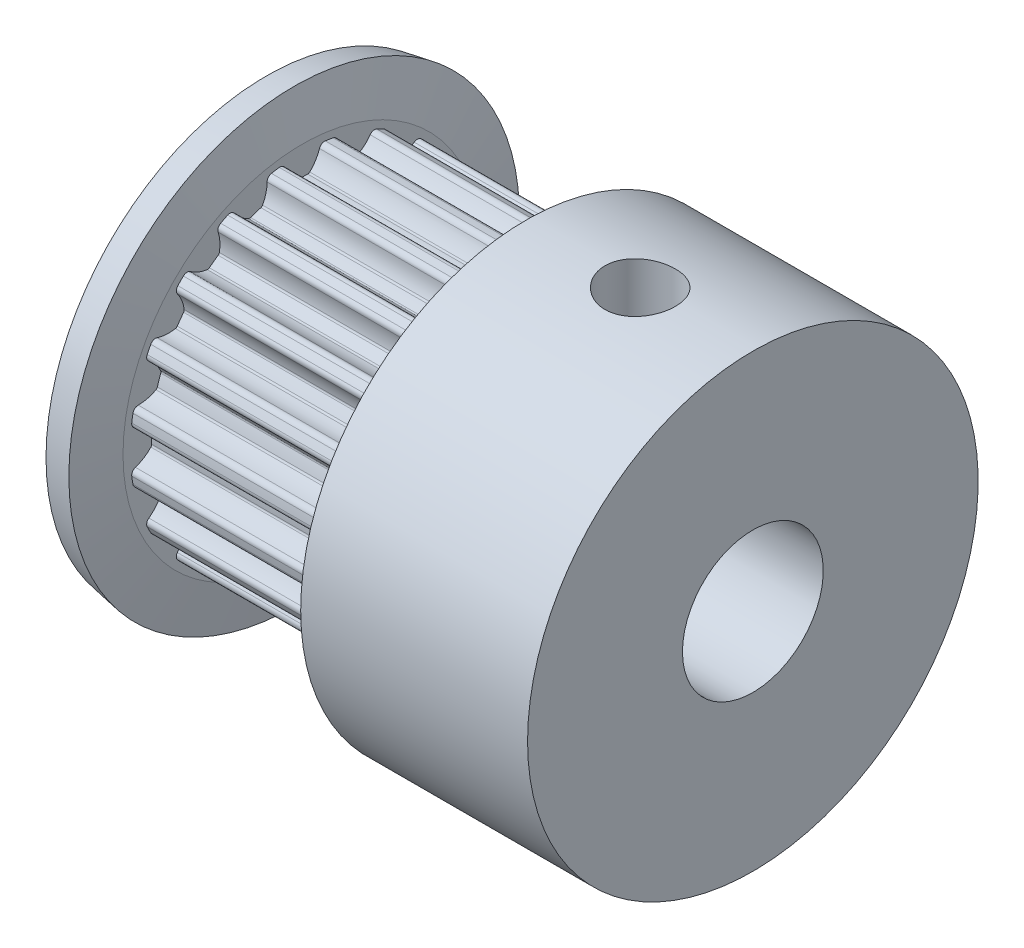
SolidWorks part; units mm, degrees
material "6061 Alloy"
ref_plane "Front Plane" through (0, 0, 0) normal (0, 0, 1) x (1, 0, 0)
ref_plane "Top Plane" through (0, 0, 0) normal (0, 1, 0) x (1, 0, 0)
ref_plane "Right Plane" through (0, 0, 0) normal (1, 0, 0) x (0, 0, -1)
ref_plane "Plane1" through (0, 0, 0) normal (0, 0, 1) x (1, 0, 0)
sketch "Sketch1" plane through (0, 0, 0) normal (0, 0, 1) x (1, 0, 0)
  line L0 (0, 5) -> (0, 2.5)
  line L1 (0, 2.5) -> (18, 2.5)
  line L2 (18, 2.5) -> (18, 8)
  line L3 (18, 8) -> (9.944, 8)
  line L4 (9.944, 8) -> (9, 6.365)
  line L5 (9, 6.365) -> (9, 6.11)
  line L6 (9, 6.11) -> (2, 6.11)
  line L7 (2, 6.11) -> (2, 6.365)
  line L8 (2, 6.365) -> (1.7117, 8)
  line L9 (1.7117, 8) -> (0.7269, 7.8264)
  line L10 (0.7269, 7.8264) -> (1, 6.2775)
  line L11 (1, 6.2775) -> (1, 5)
  line L12 (1, 5) -> (0, 5)
  line L13 (19, 0) -> (0, 0) construction
  dimension "D1" = 10
  dimension "D2" = 1
  dimension "D3" = 8
  dimension "D4" = 6.365
  dimension "D5" = 18
  dimension "D6" = 7
  dimension "D7" = 9
  dimension "D8" = 30
revolve "Revolve1" add sketch "Sketch1" angle 360 about L13
ref_plane "Plane2" through (2, 0, 0) normal (1, 0, 0) x (0, 0, -1)
sketch "Sketch2" plane through (2, 0, 0) normal (1, 0, 0) x (0, 0, -1)
  line L0 (0.8173, 6.0551) -> (0.8173, 8.1467)
  line L1 (0.8173, 8.1467) -> (-0.8173, 8.1467)
  line L2 (-0.8173, 8.1467) -> (-0.8173, 6.0551)
  arc A0 (-0.8173, 6.0551) -> (-0.6111, 5.9251) centre (-0.7919, 5.8668) cw
  arc A1 (-0.6111, 5.9251) -> (-0.2658, 5.3742) centre (0.65, 6.3317) ccw
  arc A2 (-0.2658, 5.3742) -> (-0.1931, 5.3465) centre (-0.1967, 5.4464) ccw
  arc A3 (-0.1931, 5.3465) -> (0.1931, 5.3465) centre (0, 0) cw
  arc A4 (0.1931, 5.3465) -> (0.2658, 5.3742) centre (0.1967, 5.4464) ccw
  arc A5 (0.2658, 5.3742) -> (0.6111, 5.9251) centre (-0.65, 6.3317) ccw
  arc A6 (0.6111, 5.9251) -> (0.8173, 6.0551) centre (0.7919, 5.8668) cw
extrude "Cut-Extrude1" cut sketch "Sketch2" along normal blind 7
ref_plane "Plane3" through (2, 0, 0) normal (1, 0, 0) x (0, 0, -1)
sketch "Sketch3" plane through (2, 0, 0) normal (1, 0, 0) x (0, 0, -1)
  line L0 (-1.0938, 6.0113) -> (-1.7401, 8.0005)
  line L1 (-1.7401, 8.0005) -> (-3.2948, 7.4954)
  line L2 (-3.2948, 7.4954) -> (-2.6484, 5.5062)
  arc A0 (-2.6484, 5.5062) -> (-2.4121, 5.4463) centre (-2.5661, 5.3349) cw
  arc A1 (-2.4121, 5.4463) -> (-1.9135, 5.029) centre (-1.3384, 6.2227) ccw
  arc A2 (-1.9135, 5.029) -> (-1.8358, 5.0252) centre (-1.8701, 5.1191) ccw
  arc A3 (-1.8358, 5.0252) -> (-1.4685, 5.1445) centre (0, 0) cw
  arc A4 (-1.4685, 5.1445) -> (-1.4079, 5.1933) centre (-1.496, 5.2407) ccw
  arc A5 (-1.4079, 5.1933) -> (-1.2498, 5.8239) centre (-2.5748, 5.821) ccw
  arc A6 (-1.2498, 5.8239) -> (-1.0938, 6.0113) centre (-1.0598, 5.8244) cw
extrude "Cut-Extrude2" cut sketch "Sketch3" along normal blind 7
ref_plane "Plane4" through (2, 0, 0) normal (1, 0, 0) x (0, 0, -1)
sketch "Sketch4" plane through (2, 0, 0) normal (1, 0, 0) x (0, 0, -1)
  line L0 (-2.8979, 5.3791) -> (-4.1273, 7.0712)
  line L1 (-4.1273, 7.0712) -> (-5.4497, 6.1104)
  line L2 (-5.4497, 6.1104) -> (-4.2203, 4.4183)
  arc A0 (-4.2203, 4.4183) -> (-3.9771, 4.4343) centre (-4.0891, 4.2809) cw
  arc A1 (-3.9771, 4.4343) -> (-3.3739, 4.1916) centre (-3.1958, 5.5045) ccw
  arc A2 (-3.3739, 4.1916) -> (-3.2988, 4.2119) centre (-3.3605, 4.2906) ccw
  arc A3 (-3.2988, 4.2119) -> (-2.9864, 4.4389) centre (0, 0) cw
  arc A4 (-2.9864, 4.4389) -> (-2.9438, 4.5041) centre (-3.0422, 4.5219) ccw
  arc A5 (-2.9438, 4.5041) -> (-2.9883, 5.1527) centre (-4.2476, 4.7404) ccw
  arc A6 (-2.9883, 5.1527) -> (-2.8979, 5.3791) centre (-2.8078, 5.2118) cw
extrude "Cut-Extrude3" cut sketch "Sketch4" along normal blind 7
ref_plane "Plane5" through (2, 0, 0) normal (1, 0, 0) x (0, 0, -1)
sketch "Sketch5" plane through (2, 0, 0) normal (1, 0, 0) x (0, 0, -1)
  line L0 (-4.4183, 4.2203) -> (-6.1104, 5.4497)
  line L1 (-6.1104, 5.4497) -> (-7.0712, 4.1273)
  line L2 (-7.0712, 4.1273) -> (-5.3791, 2.8979)
  arc A0 (-5.3791, 2.8979) -> (-5.1527, 2.9883) centre (-5.2118, 2.8078) cw
  arc A1 (-5.1527, 2.9883) -> (-4.5041, 2.9438) centre (-4.7404, 4.2476) ccw
  arc A2 (-4.5041, 2.9438) -> (-4.4389, 2.9864) centre (-4.5219, 3.0422) ccw
  arc A3 (-4.4389, 2.9864) -> (-4.2119, 3.2988) centre (0, 0) cw
  arc A4 (-4.2119, 3.2988) -> (-4.1916, 3.3739) centre (-4.2906, 3.3605) ccw
  arc A5 (-4.1916, 3.3739) -> (-4.4343, 3.9771) centre (-5.5045, 3.1958) ccw
  arc A6 (-4.4343, 3.9771) -> (-4.4183, 4.2203) centre (-4.2809, 4.0891) cw
extrude "Cut-Extrude4" cut sketch "Sketch5" along normal blind 7
ref_plane "Plane6" through (2, 0, 0) normal (1, 0, 0) x (0, 0, -1)
sketch "Sketch6" plane through (2, 0, 0) normal (1, 0, 0) x (0, 0, -1)
  line L0 (-5.5062, 2.6484) -> (-7.4954, 3.2948)
  line L1 (-7.4954, 3.2948) -> (-8.0005, 1.7401)
  line L2 (-8.0005, 1.7401) -> (-6.0113, 1.0938)
  arc A0 (-6.0113, 1.0938) -> (-5.8239, 1.2498) centre (-5.8244, 1.0598) cw
  arc A1 (-5.8239, 1.2498) -> (-5.1933, 1.4079) centre (-5.821, 2.5748) ccw
  arc A2 (-5.1933, 1.4079) -> (-5.1445, 1.4685) centre (-5.2407, 1.496) ccw
  arc A3 (-5.1445, 1.4685) -> (-5.0252, 1.8358) centre (0, 0) cw
  arc A4 (-5.0252, 1.8358) -> (-5.029, 1.9135) centre (-5.1191, 1.8701) ccw
  arc A5 (-5.029, 1.9135) -> (-5.4463, 2.4121) centre (-6.2227, 1.3384) ccw
  arc A6 (-5.4463, 2.4121) -> (-5.5062, 2.6484) centre (-5.3349, 2.5661) cw
extrude "Cut-Extrude5" cut sketch "Sketch6" along normal blind 7
ref_plane "Plane7" through (2, 0, 0) normal (1, 0, 0) x (0, 0, -1)
sketch "Sketch7" plane through (2, 0, 0) normal (1, 0, 0) x (0, 0, -1)
  line L0 (-6.0551, 0.8173) -> (-8.1467, 0.8173)
  line L1 (-8.1467, 0.8173) -> (-8.1467, -0.8173)
  line L2 (-8.1467, -0.8173) -> (-6.0551, -0.8173)
  arc A0 (-6.0551, -0.8173) -> (-5.9251, -0.6111) centre (-5.8668, -0.7919) cw
  arc A1 (-5.9251, -0.6111) -> (-5.3742, -0.2658) centre (-6.3317, 0.65) ccw
  arc A2 (-5.3742, -0.2658) -> (-5.3465, -0.1931) centre (-5.4464, -0.1967) ccw
  arc A3 (-5.3465, -0.1931) -> (-5.3465, 0.1931) centre (0, 0) cw
  arc A4 (-5.3465, 0.1931) -> (-5.3742, 0.2658) centre (-5.4464, 0.1967) ccw
  arc A5 (-5.3742, 0.2658) -> (-5.9251, 0.6111) centre (-6.3317, -0.65) ccw
  arc A6 (-5.9251, 0.6111) -> (-6.0551, 0.8173) centre (-5.8668, 0.7919) cw
extrude "Cut-Extrude6" cut sketch "Sketch7" along normal blind 7
ref_plane "Plane8" through (2, 0, 0) normal (1, 0, 0) x (0, 0, -1)
sketch "Sketch8" plane through (2, 0, 0) normal (1, 0, 0) x (0, 0, -1)
  line L0 (-6.0113, -1.0938) -> (-8.0005, -1.7401)
  line L1 (-8.0005, -1.7401) -> (-7.4954, -3.2948)
  line L2 (-7.4954, -3.2948) -> (-5.5062, -2.6484)
  arc A0 (-5.5062, -2.6484) -> (-5.4463, -2.4121) centre (-5.3349, -2.5661) cw
  arc A1 (-5.4463, -2.4121) -> (-5.029, -1.9135) centre (-6.2227, -1.3384) ccw
  arc A2 (-5.029, -1.9135) -> (-5.0252, -1.8358) centre (-5.1191, -1.8701) ccw
  arc A3 (-5.0252, -1.8358) -> (-5.1445, -1.4685) centre (0, 0) cw
  arc A4 (-5.1445, -1.4685) -> (-5.1933, -1.4079) centre (-5.2407, -1.496) ccw
  arc A5 (-5.1933, -1.4079) -> (-5.8239, -1.2498) centre (-5.821, -2.5748) ccw
  arc A6 (-5.8239, -1.2498) -> (-6.0113, -1.0938) centre (-5.8244, -1.0598) cw
extrude "Cut-Extrude7" cut sketch "Sketch8" along normal blind 7
ref_plane "Plane9" through (2, 0, 0) normal (1, 0, 0) x (0, 0, -1)
sketch "Sketch9" plane through (2, 0, 0) normal (1, 0, 0) x (0, 0, -1)
  line L0 (-5.3791, -2.8979) -> (-7.0712, -4.1273)
  line L1 (-7.0712, -4.1273) -> (-6.1104, -5.4497)
  line L2 (-6.1104, -5.4497) -> (-4.4183, -4.2203)
  arc A0 (-4.4183, -4.2203) -> (-4.4343, -3.9771) centre (-4.2809, -4.0891) cw
  arc A1 (-4.4343, -3.9771) -> (-4.1916, -3.3739) centre (-5.5045, -3.1958) ccw
  arc A2 (-4.1916, -3.3739) -> (-4.2119, -3.2988) centre (-4.2906, -3.3605) ccw
  arc A3 (-4.2119, -3.2988) -> (-4.4389, -2.9864) centre (0, 0) cw
  arc A4 (-4.4389, -2.9864) -> (-4.5041, -2.9438) centre (-4.5219, -3.0422) ccw
  arc A5 (-4.5041, -2.9438) -> (-5.1527, -2.9883) centre (-4.7404, -4.2476) ccw
  arc A6 (-5.1527, -2.9883) -> (-5.3791, -2.8979) centre (-5.2118, -2.8078) cw
extrude "Cut-Extrude8" cut sketch "Sketch9" along normal blind 7
ref_plane "Plane10" through (2, 0, 0) normal (1, 0, 0) x (0, 0, -1)
sketch "Sketch10" plane through (2, 0, 0) normal (1, 0, 0) x (0, 0, -1)
  line L0 (-4.2203, -4.4183) -> (-5.4497, -6.1104)
  line L1 (-5.4497, -6.1104) -> (-4.1273, -7.0712)
  line L2 (-4.1273, -7.0712) -> (-2.8979, -5.3791)
  arc A0 (-2.8979, -5.3791) -> (-2.9883, -5.1527) centre (-2.8078, -5.2118) cw
  arc A1 (-2.9883, -5.1527) -> (-2.9438, -4.5041) centre (-4.2476, -4.7404) ccw
  arc A2 (-2.9438, -4.5041) -> (-2.9864, -4.4389) centre (-3.0422, -4.5219) ccw
  arc A3 (-2.9864, -4.4389) -> (-3.2988, -4.2119) centre (0, 0) cw
  arc A4 (-3.2988, -4.2119) -> (-3.3739, -4.1916) centre (-3.3605, -4.2906) ccw
  arc A5 (-3.3739, -4.1916) -> (-3.9771, -4.4343) centre (-3.1958, -5.5045) ccw
  arc A6 (-3.9771, -4.4343) -> (-4.2203, -4.4183) centre (-4.0891, -4.2809) cw
extrude "Cut-Extrude9" cut sketch "Sketch10" along normal blind 7
ref_plane "Plane11" through (2, 0, 0) normal (1, 0, 0) x (0, 0, -1)
sketch "Sketch11" plane through (2, 0, 0) normal (1, 0, 0) x (0, 0, -1)
  line L0 (-2.6484, -5.5062) -> (-3.2948, -7.4954)
  line L1 (-3.2948, -7.4954) -> (-1.7401, -8.0005)
  line L2 (-1.7401, -8.0005) -> (-1.0938, -6.0113)
  arc A0 (-1.0938, -6.0113) -> (-1.2498, -5.8239) centre (-1.0598, -5.8244) cw
  arc A1 (-1.2498, -5.8239) -> (-1.4079, -5.1933) centre (-2.5748, -5.821) ccw
  arc A2 (-1.4079, -5.1933) -> (-1.4685, -5.1445) centre (-1.496, -5.2407) ccw
  arc A3 (-1.4685, -5.1445) -> (-1.8358, -5.0252) centre (0, 0) cw
  arc A4 (-1.8358, -5.0252) -> (-1.9135, -5.029) centre (-1.8701, -5.1191) ccw
  arc A5 (-1.9135, -5.029) -> (-2.4121, -5.4463) centre (-1.3384, -6.2227) ccw
  arc A6 (-2.4121, -5.4463) -> (-2.6484, -5.5062) centre (-2.5661, -5.3349) cw
extrude "Cut-Extrude10" cut sketch "Sketch11" along normal blind 7
ref_plane "Plane12" through (2, 0, 0) normal (1, 0, 0) x (0, 0, -1)
sketch "Sketch12" plane through (2, 0, 0) normal (1, 0, 0) x (0, 0, -1)
  line L0 (-0.8173, -6.0551) -> (-0.8173, -8.1467)
  line L1 (-0.8173, -8.1467) -> (0.8173, -8.1467)
  line L2 (0.8173, -8.1467) -> (0.8173, -6.0551)
  arc A0 (0.8173, -6.0551) -> (0.6111, -5.9251) centre (0.7919, -5.8668) cw
  arc A1 (0.6111, -5.9251) -> (0.2658, -5.3742) centre (-0.65, -6.3317) ccw
  arc A2 (0.2658, -5.3742) -> (0.1931, -5.3465) centre (0.1967, -5.4464) ccw
  arc A3 (0.1931, -5.3465) -> (-0.1931, -5.3465) centre (0, 0) cw
  arc A4 (-0.1931, -5.3465) -> (-0.2658, -5.3742) centre (-0.1967, -5.4464) ccw
  arc A5 (-0.2658, -5.3742) -> (-0.6111, -5.9251) centre (0.65, -6.3317) ccw
  arc A6 (-0.6111, -5.9251) -> (-0.8173, -6.0551) centre (-0.7919, -5.8668) cw
extrude "Cut-Extrude11" cut sketch "Sketch12" along normal blind 7
ref_plane "Plane13" through (2, 0, 0) normal (1, 0, 0) x (0, 0, -1)
sketch "Sketch13" plane through (2, 0, 0) normal (1, 0, 0) x (0, 0, -1)
  line L0 (1.0938, -6.0113) -> (1.7401, -8.0005)
  line L1 (1.7401, -8.0005) -> (3.2948, -7.4954)
  line L2 (3.2948, -7.4954) -> (2.6484, -5.5062)
  arc A0 (2.6484, -5.5062) -> (2.4121, -5.4463) centre (2.5661, -5.3349) cw
  arc A1 (2.4121, -5.4463) -> (1.9135, -5.029) centre (1.3384, -6.2227) ccw
  arc A2 (1.9135, -5.029) -> (1.8358, -5.0252) centre (1.8701, -5.1191) ccw
  arc A3 (1.8358, -5.0252) -> (1.4685, -5.1445) centre (0, 0) cw
  arc A4 (1.4685, -5.1445) -> (1.4079, -5.1933) centre (1.496, -5.2407) ccw
  arc A5 (1.4079, -5.1933) -> (1.2498, -5.8239) centre (2.5748, -5.821) ccw
  arc A6 (1.2498, -5.8239) -> (1.0938, -6.0113) centre (1.0598, -5.8244) cw
extrude "Cut-Extrude12" cut sketch "Sketch13" along normal blind 7
ref_plane "Plane14" through (2, 0, 0) normal (1, 0, 0) x (0, 0, -1)
sketch "Sketch14" plane through (2, 0, 0) normal (1, 0, 0) x (0, 0, -1)
  line L0 (2.8979, -5.3791) -> (4.1273, -7.0712)
  line L1 (4.1273, -7.0712) -> (5.4497, -6.1104)
  line L2 (5.4497, -6.1104) -> (4.2203, -4.4183)
  arc A0 (4.2203, -4.4183) -> (3.9771, -4.4343) centre (4.0891, -4.2809) cw
  arc A1 (3.9771, -4.4343) -> (3.3739, -4.1916) centre (3.1958, -5.5045) ccw
  arc A2 (3.3739, -4.1916) -> (3.2988, -4.2119) centre (3.3605, -4.2906) ccw
  arc A3 (3.2988, -4.2119) -> (2.9864, -4.4389) centre (0, 0) cw
  arc A4 (2.9864, -4.4389) -> (2.9438, -4.5041) centre (3.0422, -4.5219) ccw
  arc A5 (2.9438, -4.5041) -> (2.9883, -5.1527) centre (4.2476, -4.7404) ccw
  arc A6 (2.9883, -5.1527) -> (2.8979, -5.3791) centre (2.8078, -5.2118) cw
extrude "Cut-Extrude13" cut sketch "Sketch14" along normal blind 7
ref_plane "Plane15" through (2, 0, 0) normal (1, 0, 0) x (0, 0, -1)
sketch "Sketch15" plane through (2, 0, 0) normal (1, 0, 0) x (0, 0, -1)
  line L0 (4.4183, -4.2203) -> (6.1104, -5.4497)
  line L1 (6.1104, -5.4497) -> (7.0712, -4.1273)
  line L2 (7.0712, -4.1273) -> (5.3791, -2.8979)
  arc A0 (5.3791, -2.8979) -> (5.1527, -2.9883) centre (5.2118, -2.8078) cw
  arc A1 (5.1527, -2.9883) -> (4.5041, -2.9438) centre (4.7404, -4.2476) ccw
  arc A2 (4.5041, -2.9438) -> (4.4389, -2.9864) centre (4.5219, -3.0422) ccw
  arc A3 (4.4389, -2.9864) -> (4.2119, -3.2988) centre (0, 0) cw
  arc A4 (4.2119, -3.2988) -> (4.1916, -3.3739) centre (4.2906, -3.3605) ccw
  arc A5 (4.1916, -3.3739) -> (4.4343, -3.9771) centre (5.5045, -3.1958) ccw
  arc A6 (4.4343, -3.9771) -> (4.4183, -4.2203) centre (4.2809, -4.0891) cw
extrude "Cut-Extrude14" cut sketch "Sketch15" along normal blind 7
ref_plane "Plane16" through (2, 0, 0) normal (1, 0, 0) x (0, 0, -1)
sketch "Sketch16" plane through (2, 0, 0) normal (1, 0, 0) x (0, 0, -1)
  line L0 (5.5062, -2.6484) -> (7.4954, -3.2948)
  line L1 (7.4954, -3.2948) -> (8.0005, -1.7401)
  line L2 (8.0005, -1.7401) -> (6.0113, -1.0938)
  arc A0 (6.0113, -1.0938) -> (5.8239, -1.2498) centre (5.8244, -1.0598) cw
  arc A1 (5.8239, -1.2498) -> (5.1933, -1.4079) centre (5.821, -2.5748) ccw
  arc A2 (5.1933, -1.4079) -> (5.1445, -1.4685) centre (5.2407, -1.496) ccw
  arc A3 (5.1445, -1.4685) -> (5.0252, -1.8358) centre (0, 0) cw
  arc A4 (5.0252, -1.8358) -> (5.029, -1.9135) centre (5.1191, -1.8701) ccw
  arc A5 (5.029, -1.9135) -> (5.4463, -2.4121) centre (6.2227, -1.3384) ccw
  arc A6 (5.4463, -2.4121) -> (5.5062, -2.6484) centre (5.3349, -2.5661) cw
extrude "Cut-Extrude15" cut sketch "Sketch16" along normal blind 7
ref_plane "Plane17" through (2, 0, 0) normal (1, 0, 0) x (0, 0, -1)
sketch "Sketch17" plane through (2, 0, 0) normal (1, 0, 0) x (0, 0, -1)
  line L0 (6.0551, -0.8173) -> (8.1467, -0.8173)
  line L1 (8.1467, -0.8173) -> (8.1467, 0.8173)
  line L2 (8.1467, 0.8173) -> (6.0551, 0.8173)
  arc A0 (6.0551, 0.8173) -> (5.9251, 0.6111) centre (5.8668, 0.7919) cw
  arc A1 (5.9251, 0.6111) -> (5.3742, 0.2658) centre (6.3317, -0.65) ccw
  arc A2 (5.3742, 0.2658) -> (5.3465, 0.1931) centre (5.4464, 0.1967) ccw
  arc A3 (5.3465, 0.1931) -> (5.3465, -0.1931) centre (0, 0) cw
  arc A4 (5.3465, -0.1931) -> (5.3742, -0.2658) centre (5.4464, -0.1967) ccw
  arc A5 (5.3742, -0.2658) -> (5.9251, -0.6111) centre (6.3317, 0.65) ccw
  arc A6 (5.9251, -0.6111) -> (6.0551, -0.8173) centre (5.8668, -0.7919) cw
extrude "Cut-Extrude16" cut sketch "Sketch17" along normal blind 7
ref_plane "Plane18" through (2, 0, 0) normal (1, 0, 0) x (0, 0, -1)
sketch "Sketch18" plane through (2, 0, 0) normal (1, 0, 0) x (0, 0, -1)
  line L0 (6.0113, 1.0938) -> (8.0005, 1.7401)
  line L1 (8.0005, 1.7401) -> (7.4954, 3.2948)
  line L2 (7.4954, 3.2948) -> (5.5062, 2.6484)
  arc A0 (5.5062, 2.6484) -> (5.4463, 2.4121) centre (5.3349, 2.5661) cw
  arc A1 (5.4463, 2.4121) -> (5.029, 1.9135) centre (6.2227, 1.3384) ccw
  arc A2 (5.029, 1.9135) -> (5.0252, 1.8358) centre (5.1191, 1.8701) ccw
  arc A3 (5.0252, 1.8358) -> (5.1445, 1.4685) centre (0, 0) cw
  arc A4 (5.1445, 1.4685) -> (5.1933, 1.4079) centre (5.2407, 1.496) ccw
  arc A5 (5.1933, 1.4079) -> (5.8239, 1.2498) centre (5.821, 2.5748) ccw
  arc A6 (5.8239, 1.2498) -> (6.0113, 1.0938) centre (5.8244, 1.0598) cw
extrude "Cut-Extrude17" cut sketch "Sketch18" along normal blind 7
ref_plane "Plane19" through (2, 0, 0) normal (1, 0, 0) x (0, 0, -1)
sketch "Sketch19" plane through (2, 0, 0) normal (1, 0, 0) x (0, 0, -1)
  line L0 (5.3791, 2.8979) -> (7.0712, 4.1273)
  line L1 (7.0712, 4.1273) -> (6.1104, 5.4497)
  line L2 (6.1104, 5.4497) -> (4.4183, 4.2203)
  arc A0 (4.4183, 4.2203) -> (4.4343, 3.9771) centre (4.2809, 4.0891) cw
  arc A1 (4.4343, 3.9771) -> (4.1916, 3.3739) centre (5.5045, 3.1958) ccw
  arc A2 (4.1916, 3.3739) -> (4.2119, 3.2988) centre (4.2906, 3.3605) ccw
  arc A3 (4.2119, 3.2988) -> (4.4389, 2.9864) centre (0, 0) cw
  arc A4 (4.4389, 2.9864) -> (4.5041, 2.9438) centre (4.5219, 3.0422) ccw
  arc A5 (4.5041, 2.9438) -> (5.1527, 2.9883) centre (4.7404, 4.2476) ccw
  arc A6 (5.1527, 2.9883) -> (5.3791, 2.8979) centre (5.2118, 2.8078) cw
extrude "Cut-Extrude18" cut sketch "Sketch19" along normal blind 7
ref_plane "Plane20" through (2, 0, 0) normal (1, 0, 0) x (0, 0, -1)
sketch "Sketch20" plane through (2, 0, 0) normal (1, 0, 0) x (0, 0, -1)
  line L0 (4.2203, 4.4183) -> (5.4497, 6.1104)
  line L1 (5.4497, 6.1104) -> (4.1273, 7.0712)
  line L2 (4.1273, 7.0712) -> (2.8979, 5.3791)
  arc A0 (2.8979, 5.3791) -> (2.9883, 5.1527) centre (2.8078, 5.2118) cw
  arc A1 (2.9883, 5.1527) -> (2.9438, 4.5041) centre (4.2476, 4.7404) ccw
  arc A2 (2.9438, 4.5041) -> (2.9864, 4.4389) centre (3.0422, 4.5219) ccw
  arc A3 (2.9864, 4.4389) -> (3.2988, 4.2119) centre (0, 0) cw
  arc A4 (3.2988, 4.2119) -> (3.3739, 4.1916) centre (3.3605, 4.2906) ccw
  arc A5 (3.3739, 4.1916) -> (3.9771, 4.4343) centre (3.1958, 5.5045) ccw
  arc A6 (3.9771, 4.4343) -> (4.2203, 4.4183) centre (4.0891, 4.2809) cw
extrude "Cut-Extrude19" cut sketch "Sketch20" along normal blind 7
ref_plane "Plane21" through (2, 0, 0) normal (1, 0, 0) x (0, 0, -1)
sketch "Sketch21" plane through (2, 0, 0) normal (1, 0, 0) x (0, 0, -1)
  line L0 (2.6484, 5.5062) -> (3.2948, 7.4954)
  line L1 (3.2948, 7.4954) -> (1.7401, 8.0005)
  line L2 (1.7401, 8.0005) -> (1.0938, 6.0113)
  arc A0 (1.0938, 6.0113) -> (1.2498, 5.8239) centre (1.0598, 5.8244) cw
  arc A1 (1.2498, 5.8239) -> (1.4079, 5.1933) centre (2.5748, 5.821) ccw
  arc A2 (1.4079, 5.1933) -> (1.4685, 5.1445) centre (1.496, 5.2407) ccw
  arc A3 (1.4685, 5.1445) -> (1.8358, 5.0252) centre (0, 0) cw
  arc A4 (1.8358, 5.0252) -> (1.9135, 5.029) centre (1.8701, 5.1191) ccw
  arc A5 (1.9135, 5.029) -> (2.4121, 5.4463) centre (1.3384, 6.2227) ccw
  arc A6 (2.4121, 5.4463) -> (2.6484, 5.5062) centre (2.5661, 5.3349) cw
extrude "Cut-Extrude20" cut sketch "Sketch21" along normal blind 7
ref_plane "Plane22" through (0, 8, 0) normal (0, 1, 0) x (1, 0, 0)
hole_wizard "M3x0.5 Tapped Hole1" positions "Sketch23" profile "Sketch22" tap size "M3x0.5" standard "ANSI Metric"
sketch "Sketch23" plane through (0, 8, 0) normal (0, 1, 0) x (1, 0, 0)
  line L0 (18, -8) -> (18, 8) construction
  point P0 (14, 0)
  dimension "D1" = 4
sketch "Sketch22" plane through (14, 8, 0) normal (1, 0, 0) x (0, 0, 1)
  line L0 (0, 0) -> (0, 5.5)
  line L1 (0, 5.5) -> (1.25, 5.5)
  line L2 (1.25, 5.5) -> (1.25, 0)
  line L5 (1.25, 0) -> (0, 0)
  line L11 (0, -6.35) -> (0, 107.95) construction
  dimension "Thru Tap Drill Dia." = 2.5
  dimension "Thru Tap Drill Depth" = 5.5
cosmetic thread "Hole Thread1" parameters "D2"=3
